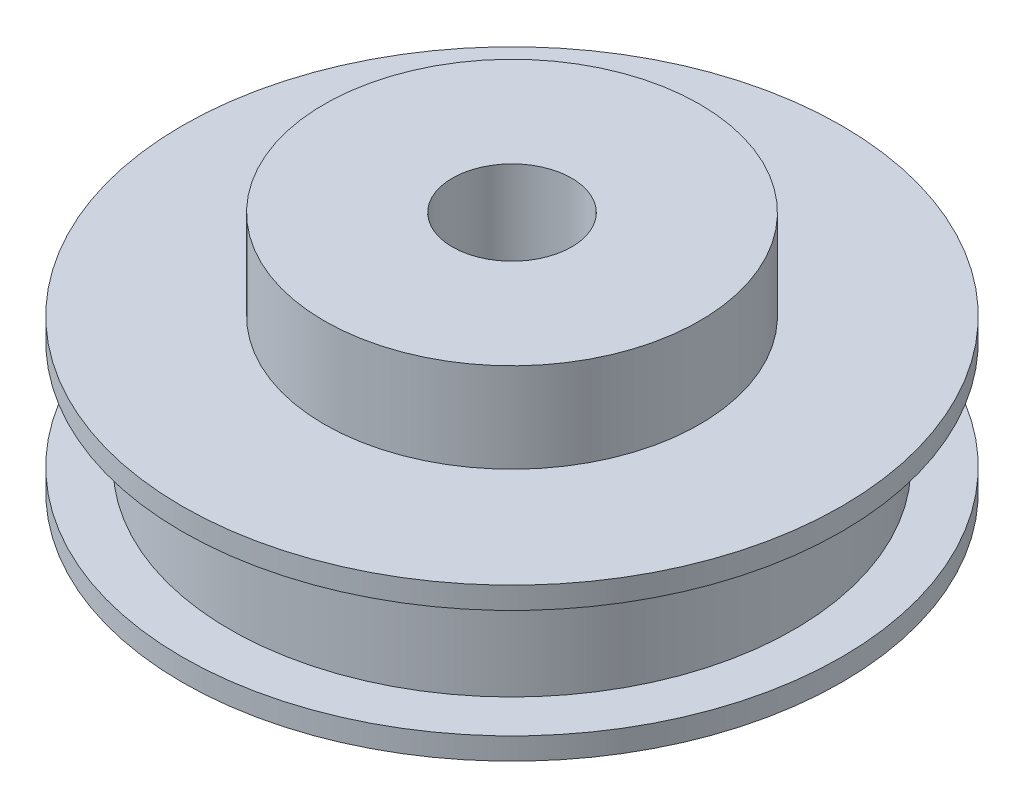
SolidWorks part; units mm, degrees
ref_plane "Front Plane" through (0, 0, 0) normal (0, 0, 1) x (1, 0, 0)
ref_plane "Top Plane" through (0, 0, 0) normal (0, 1, 0) x (1, 0, 0)
ref_plane "Right Plane" through (0, 0, 0) normal (1, 0, 0) x (0, 0, -1)
sketch "Sketch1" plane through (0, 0, 0) normal (0, 1, 0) x (1, 0, 0)
  circle A0 centre (0, 0) radius 21.971
  dimension "D1" = 43.942
extrude "Boss-Extrude1" add sketch "Sketch1" along normal blind 10.16
sketch "Sketch2" plane through (0, 0, 0) normal (0, 0, 1) x (1, 0, 0)
  line L0 (-21.971, 10.16) -> (-21.971, 0) construction
  line L1 (-21.971, 8.6995) -> (-21.971, 1.4605)
  line L2 (-21.971, 1.4605) -> (-18.796, 1.4605)
  line L3 (-18.796, 1.4605) -> (-18.796, 8.6995)
  line L4 (-18.796, 8.6995) -> (-21.971, 8.6995)
  line L5 (-18.796, 8.6995) -> (-18.796, 10.16) construction
  line L6 (-18.796, 10.16) -> (-21.971, 10.16) construction
  line L7 (-21.971, 0) -> (-18.796, 0) construction
  line L8 (-18.796, 0) -> (-18.796, 1.4605) construction
  line L9 (0, 0) -> (0, 50000) construction
  dimension "D1" = 3.175
  dimension "D2" = 7.239
revolve "Cut-Revolve1" cut sketch "Sketch2" angle 360 about L9
sketch "Sketch3" plane through (0, 10.16, 0) normal (0, 1, 0) x (1, 0, 0)
  circle A0 centre (0, 0) radius 12.5095
  dimension "D1" = 25.019
extrude "Boss-Extrude2" add sketch "Sketch3" along normal blind 5.969
sketch "Sketch4" plane through (0, 16.129, 0) normal (0, 1, 0) x (1, 0, 0)
  circle A0 centre (0, 0) radius 3.9751
  dimension "D1" = 7.9502
extrude "Cut-Extrude1" cut sketch "Sketch4" against normal through all
sketch "Sketch5" plane through (0, 16.129, 0) normal (0, 1, 0) x (1, 0, 0)
  point P0 (0, 0)
